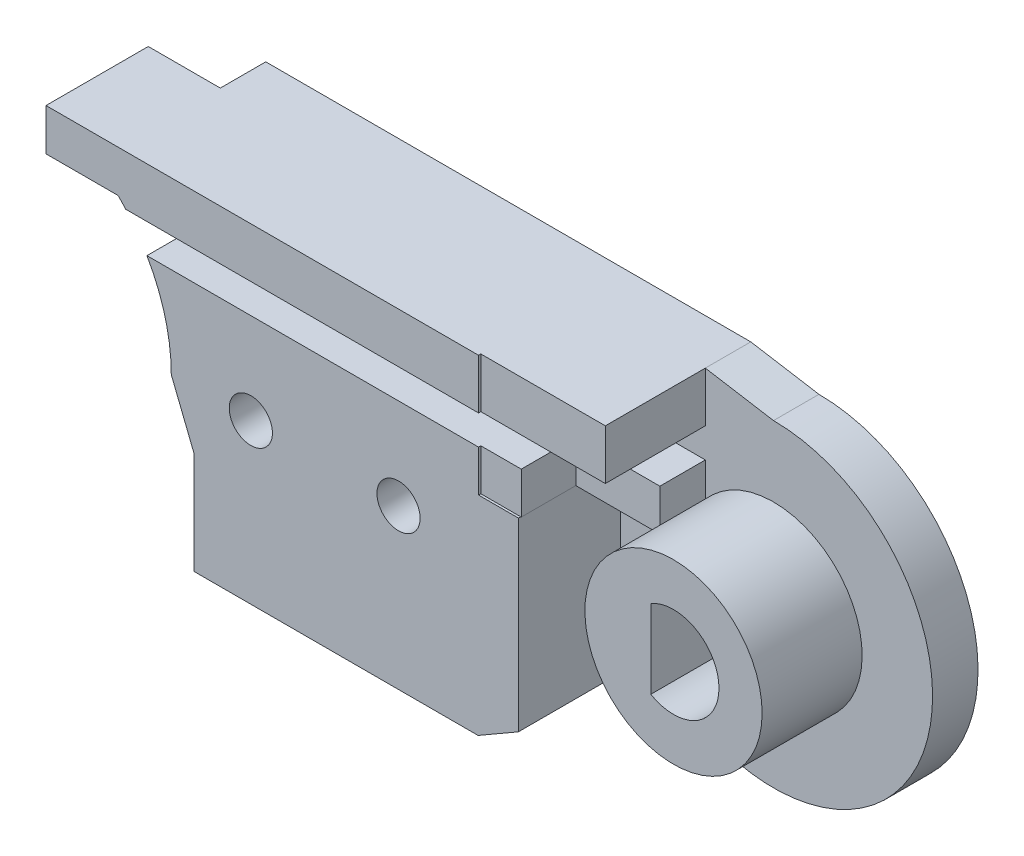
SolidWorks part; units mm, degrees
ref_plane "Front Plane" through (0, 0, 0) normal (0, 0, 1) x (1, 0, 0)
ref_plane "Top Plane" through (0, 0, 0) normal (0, 1, 0) x (1, 0, 0)
ref_plane "Right Plane" through (0, 0, 0) normal (1, 0, 0) x (0, 0, -1)
sketch "Sketch3" plane through (0, 0, 0) normal (0, 0, 1) x (1, 0, 0)
  line L7 (8, 0) -> (9, -2.5)
  line L11 (30, 7) -> (27, 7.5)
  line L13 (0, 7) -> (0, 7.5) construction
  line L14 (0, 7.5) -> (-22.3287, 7.5) construction
  line L15 (0, 5.3) -> (-14, 5.3) construction
  line L16 (0, 4) -> (-14, 4) construction
  line L17 (-14, 4) -> (-14, 5.3) construction
  line L18 (5.6569, 5.6569) -> (5.6569, 7.5)
  line L19 (5.6569, 7.5) -> (27, 7.5)
  line L20 (21.5, -7) -> (9, -7)
  line L21 (9, -7) -> (9, -2.5)
  line L23 (25.0503, -4.9497) -> (21.5, -7)
  arc A4 (8, 0) -> (5.6569, 5.6569) centre (0, 0) ccw
  arc A5 (25.0503, -4.9497) -> (30, 7) centre (30, 0) ccw
  circle A6 centre (0, 0) radius 7 construction
  circle A7 centre (0, 0) radius 3.9 construction
  circle A8 centre (0, 0) radius 5.3 construction
  circle A9 centre (0, 0) radius 4 construction
  dimension "D10" = 0.5
  dimension "D17" = 14
  dimension "D5" = 135
  dimension "D6" = 12.5
  dimension "D7" = 4.5
  dimension "D8" = 1
  dimension "D9" = 45
  dimension "D11" = 1.8431
  dimension "D12" = 30
  dimension "D14" = 3
extrude "Boss-Extrude1" add sketch "Sketch3" along normal blind 2 contours A5 L11 L19 L18 A4 L7 L21 L20 L23
sketch "Sketch20" plane through (0, 0, 0) normal (0, 0, 1) x (1, 0, 0)
  line L0 (0, 7) -> (0, 7.5) construction
  line L1 (0, 7.5) -> (-19.4737, 7.5) construction
  line L2 (0, 5.3) -> (-14, 5.3) construction
  line L3 (0, 4) -> (-14, 4) construction
  line L4 (-14, 4) -> (-14, 5.3) construction
  line L5 (0, 5.3) -> (17.4849, 5.3) construction
  line L6 (17.4849, 5.3) -> (17.4849, 4) construction
  line L7 (17.4849, 4) -> (0, 4) construction
  line L8 (-2.5, 7.5) -> (-2.5, 2.868) construction
  circle A0 centre (0, 0) radius 7 construction
  circle A1 centre (0, 0) radius 3.9 construction
  circle A3 centre (0, 0) radius 5.3 construction
  circle A4 centre (0, 0) radius 4 construction
  circle A5 centre (0, 0) radius 2 construction
  dimension "D1" = 0
  dimension "D2" = 2.5
ref_plane "Plane1" through (0, 0, 2) normal (0, 0, 1) x (1, 0, 0)
sketch "Sketch4" plane through (0, 0, 2) normal (0, 0, 1) x (1, 0, 0)
  line L4 (5.6569, 5.6569) -> (5.6569, 7.5)
  line L5 (5.6569, 5.6569) -> (5.6569, 7.5) construction
  line L6 (5.6569, 7.5) -> (21.5, 7.5)
  line L10 (8, 0) -> (9, -2.5)
  line L11 (9, -2.5) -> (9, -7)
  line L12 (9, -7) -> (21.5, -7)
  line L13 (21.5, -7) -> (21.5, 7.5)
  arc A0 (8, 0) -> (5.6569, 5.6569) centre (0, 0) ccw construction
  arc A3 (8, 0) -> (5.6569, 5.6569) centre (0, 0) ccw
sketch "Sketch22" plane through (0, 0, 2) normal (0, 0, 1) x (1, 0, 0)
  line L0 (5.6569, 5.6569) -> (2.4868, 5.6569)
  line L1 (5.6569, 7.5) -> (21.5, 7.5)
  line L2 (5.6569, 7.5) -> (2.4868, 7.5)
  line L3 (2.4868, 7.5) -> (2.4868, 5.6569)
  line L6 (8, 0) -> (9, -2.5)
  line L7 (9, -2.5) -> (9, -7)
  line L8 (9, -7) -> (21.5, -7)
  line L10 (21.5, 7.5) -> (27, 7.5)
  line L11 (27, 7.5) -> (27, 2.172)
  line L12 (27, 2.172) -> (23.2751, 2.172)
  line L13 (21.5, -7) -> (23.2751, -5.9749)
  line L14 (25.0503, -4.9497) -> (21.5, -7) construction
  line L15 (23.2751, -5.9749) -> (23.2751, 2.172)
  arc A0 (8, 0) -> (5.6569, 5.6569) centre (0, 0) ccw
extrude "Boss-Extrude6" add sketch "Sketch22" along normal blind 4.5
sketch "Sketch25" plane through (0, 0, 2) normal (0, 0, 1) x (1, 0, 0)
  line L0 (0, 5.3) -> (18.0981, 5.3) construction
  line L1 (0, 4) -> (18.0981, 4) construction
  line L2 (18.0981, 4) -> (18.0981, 5.3) construction
sketch "Sketch26" plane through (0, 0, 2) normal (0, 0, 1) x (1, 0, 0)
  line L1 (18.0981, 5.3) -> (2.5301, 5.3)
  line L2 (18.0981, 4) -> (2.5301, 4)
  line L3 (2.5301, 5.3) -> (2.5301, 4)
  line L4 (18.0981, 5.3) -> (27, 5.3)
  line L5 (27, 2.172) -> (27, 7.5) construction
  line L6 (27, 5.3) -> (27, 4)
  line L7 (27, 4) -> (18.0981, 4)
extrude "Cut-Extrude6" cut sketch "Sketch26" along normal blind 4.5
ref_plane "Plane18" through (0, 0, 6.5) normal (0, 0, 1) x (1, 0, 0)
sketch "Sketch31" plane through (0, 0, 6.5) normal (0, 0, 1) x (1, 0, 0)
  line L0 (2.4327, 5.6569) -> (0, 5.6569)
  line L4 (9, -5.6569) -> (0, -5.6569)
  line L5 (2.4327, 5.6569) -> (2.4868, 7.5)
  line L12 (9, -7) -> (9, -5.6569)
  line L13 (9, -2.5) -> (9, -7) construction
  line L16 (27, 7.5) -> (27, 2.172)
  line L17 (27, 2.172) -> (23.2751, 2.172)
  line L18 (23.2751, -5.9749) -> (23.2751, 2.172)
  line L19 (27, 7.5) -> (2.4868, 7.5)
  line L20 (9, -7) -> (21.5, -7)
  line L21 (21.5, -7) -> (23.2751, -5.9749)
  arc A0 (0, 5.6569) -> (0, -5.6569) centre (0, 0) ccw
  dimension "D1" = 5.6569
extrude "Boss-Extrude14" add sketch "Sketch31" along normal blind 2.3 separate body
sketch "Sketch32" plane through (0, 0, 8.8) normal (0, 0, 1) x (1, 0, 0)
  circle A0 centre (0, 0) radius 2.1
extrude "Cut-Extrude7" cut sketch "Sketch32" against normal blind 2.3
sketch "Sketch33" plane through (0, 0, 8.8) normal (0, 0, 1) x (1, 0, 0)
  line L4 (9, -5.6569) -> (9, -7)
  line L11 (9, -7) -> (21.5, -7)
  line L15 (21.5, -7) -> (21.5, -5.6569)
  line L16 (21.5, -5.6569) -> (9, -5.6569)
  line L17 (2.4868, 7.5) -> (21.5, 7.5)
  line L18 (27, 7.5) -> (2.4868, 7.5) construction
  line L19 (2.4868, 7.5) -> (2.4327, 5.6569)
  line L20 (2.4327, 5.6569) -> (21.5, 5.6569)
  line L21 (21.5, 5.6569) -> (21.5, 7.5)
extrude "Boss-Extrude15" add sketch "Sketch33" along normal blind 1.2
sketch "Sketch34" plane through (0, 0, 2) normal (0, 0, 1) x (1, 0, 0)
  line L0 (30, 5.3) -> (18.0981, 5.3) construction
  line L1 (30, 4) -> (18.0981, 4) construction
  circle A0 centre (30, 0) radius 2 construction
  circle A1 centre (30, 0) radius 5.3 construction
  circle A2 centre (30, 0) radius 4 construction
sketch "Sketch35" plane through (0, 0, 8.8) normal (0, 0, 1) x (1, 0, 0)
  line L0 (27, 2.172) -> (27, 7.5)
  line L1 (27, 2.172) -> (21.5204, 2.172)
  line L2 (27, 7.5) -> (21.5204, 7.5)
  line L3 (21.5204, 2.172) -> (21.5204, 7.5)
  line L4 (27, 2.172) -> (27, 7.5) construction
  line L5 (27, 7.5) -> (21.5, 7.5) construction
  dimension "D1" = 0
extrude "Cut-Extrude8" cut sketch "Sketch35" against normal blind 2.4
sketch "Sketch36" plane through (0, 0, 6.4) normal (0, 0, 1) x (1, 0, 0)
  line L0 (27, 2.172) -> (27, 4)
  line L1 (27, 2.172) -> (23.3, 2.172)
  line L2 (27, 4) -> (23.3, 4)
  line L3 (23.3, 2.172) -> (23.3, 4)
  line L4 (21.5, -7) -> (21.5, 7.5) construction
  dimension "D1" = 1.8
extrude "Cut-Extrude9" cut sketch "Sketch36" against normal blind 2.4
sketch "Sketch37" plane through (0, 0, 2) normal (0, 0, 1) x (1, 0, 0)
  circle A0 centre (30, 0) radius 3.9
extrude "Boss-Extrude16" add sketch "Sketch37" along normal blind 4.4
sketch "Sketch39" plane through (0, 0, 6.4) normal (0, 0, 1) x (1, 0, 0)
  line L0 (29, 1.7321) -> (29, -1.7321)
  arc A0 (29, -1.7321) -> (29, 1.7321) centre (30, 0) ccw
  dimension "D2" = 4
  dimension "D1" = 1
extrude "Cut-Extrude10" cut sketch "Sketch39" against normal through all
sketch "Sketch43" plane through (0, 0, 8.8) normal (0, 0, 1) x (1, 0, 0)
  line L2 (0, -5.6569) -> (9, -5.6569) construction
  circle A0 centre (11.5, 0) radius 2.5
  circle A1 centre (18, 0) radius 2.5
  dimension "D1" = 2.5
  dimension "D3" = 5
  dimension "D4" = 6.5
  dimension "D2" = 5.6569
extrude "Boss-Extrude17" add sketch "Sketch43" along normal blind 1.2
sketch "Sketch44" plane through (0, 0, 10) normal (0, 0, 1) x (1, 0, 0)
  circle A0 centre (11.5, 0) radius 0.95
  circle A1 centre (18, 0) radius 0.95
  dimension "D1" = 1.9
  dimension "D2" = 1.9
extrude "Cut-Extrude11" cut sketch "Sketch44" against normal through all
sketch "Sketch45" plane through (0, 0, 0) normal (0, 0, -1) x (-1, 0, 0)
  circle A0 centre (-11.5, 0) radius 2
  circle A1 centre (-18, 0) radius 2
extrude "Cut-Extrude12" cut sketch "Sketch45" against normal blind 4.5
ref_plane "Plane17" through (0, 0, 10) normal (0, 0, 1) x (1, 0, 0)
sketch "Sketch48" plane through (0, 0, 2) normal (0, 0, 1) x (1, 0, 0)
  circle A0 centre (30, 0) radius 5 construction
sketch "Sketch51" plane through (0, 0, 10) normal (0, 0, 1) x (1, 0, 0)
  line L0 (18.2355, 5.6569) -> (27.0112, -4.8677) construction
  line L1 (2.4327, 5.6569) -> (21.5, 5.6569) construction
sketch "Sketch52" plane through (0, 5.6569, 0) normal (0, -1, 0) x (1, 0, 0)
  circle A0 centre (18.2355, 10) radius 0.75
extrude "Cut-Extrude13" cut sketch "Sketch52" along direction (0.6404, -0.768, 0) on the side against the normal blind 10
split "Split1" trim tools "Plane18" bodies to split 129 133 resulting bodies 135 136
delete or keep bodies "Body-Delete/Keep 1" type delete bodies bodies 136
